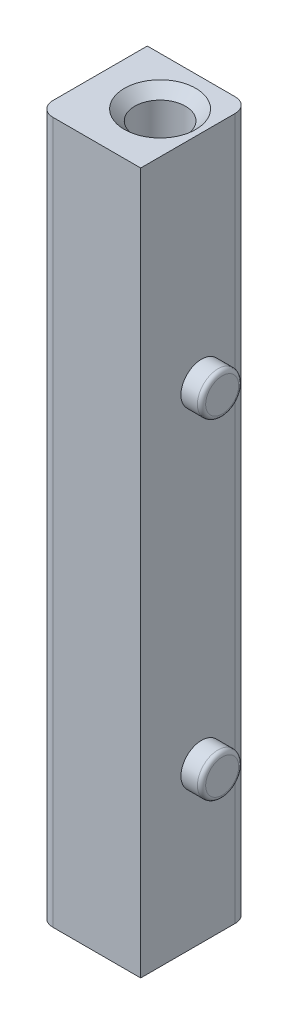
SolidWorks part; units mm, degrees
material "ABS"
ref_plane "Front Plane" through (0, 0, 0) normal (0, 0, 1) x (1, 0, 0)
ref_plane "Top Plane" through (0, 0, 0) normal (0, 1, 0) x (1, 0, 0)
ref_plane "Right Plane" through (0, 0, 0) normal (1, 0, 0) x (0, 0, -1)
sketch "Sketch1" plane through (0, 0, 0) normal (0, 1, 0) x (1, 0, 0)
  line L1 (-7.493, 5.9182) -> (5.1054, 5.9182)
  line L2 (-7.493, 5.9182) -> (-7.493, -7.493)
  line L3 (-7.493, -7.493) -> (5.1054, -7.493)
  line L4 (5.1054, 5.9182) -> (5.1054, -7.493)
  dimension "D1" = 13.4112
  dimension "D2" = 12.5984
  dimension "D3" = 5.9182
  dimension "D4" = 5.1054
extrude "Boss-Extrude1" add sketch "Sketch1" along normal blind 46.99 and the other way blind 39.37
sketch "Sketch2" plane through (0, 46.99, 0) normal (0, 1, 0) x (1, 0, 0)
  circle A0 centre (0, 0) radius 3.1242
  dimension "D1" = 6.2484
extrude "Cut-Extrude1" cut sketch "Sketch2" against normal through all
sketch "Sketch4" plane through (5.1054, 0, 0) normal (1, 0, 0) x (0, 0, -1)
  line L0 (0, 0) -> (-6.723, 0) construction
  line L1 (0, -39.37) -> (0, -45.321) construction
  circle A0 centre (0, -20.32) radius 2.54
  dimension "D1" = 5.08
  dimension "D2" = 20.32
extrude "Boss-Extrude2" add sketch "Sketch4" along normal blind 2.54
fillet "Fillet2" radius 0.508 1 edges at (7.6454, -20.32, -2.54)
mirror "Mirror1" about plane through (0, 0, 0) normal (0, 1, 0) of "Fillet2", "Boss-Extrude2"
fillet "Fillet1" radius 1.778 2 edges at (-7.493, 3.81, 7.493) (5.1054, 3.81, -5.9182)
chamfer "Chamfer1" distance 1.27 angle 45 1 edges at (0, 46.99, 3.1242)
